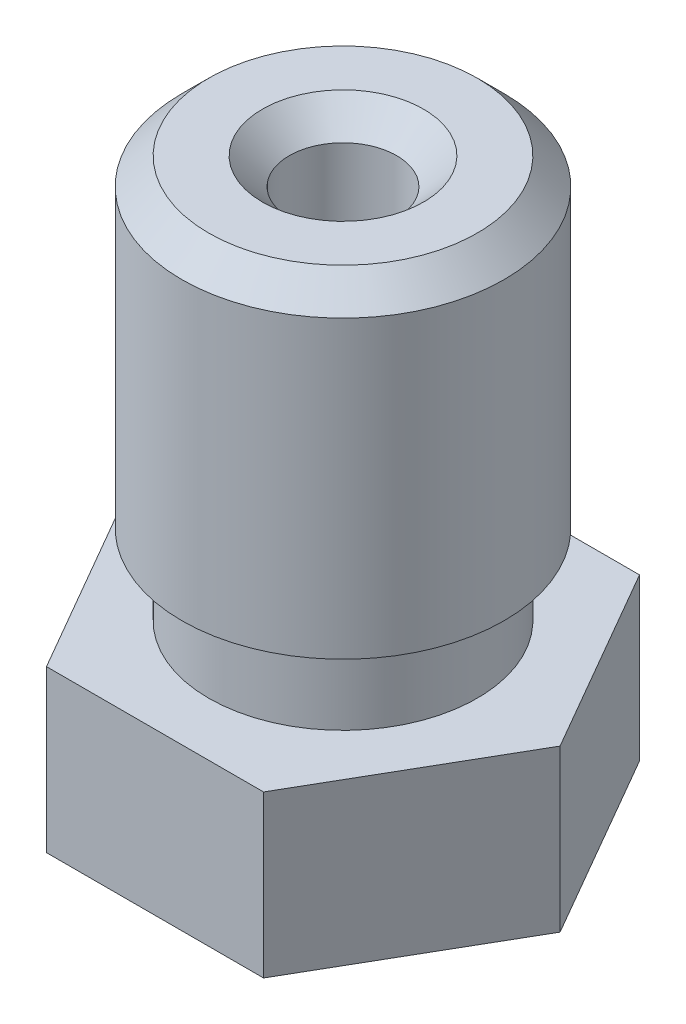
SolidWorks part; units mm, degrees
material "Brass"
ref_plane "Front Plane" through (0, 0, 0) normal (0, 0, 1) x (1, 0, 0)
ref_plane "Top Plane" through (0, 0, 0) normal (0, 1, 0) x (1, 0, 0)
ref_plane "Right Plane" through (0, 0, 0) normal (1, 0, 0) x (0, 0, -1)
ref_plane "Plane1" through (0, 0, 0) normal (0, -1, 0) x (1, 0, 0)
sketch "Sketch1" plane through (0, 0, 0) normal (0, -1, 0) x (1, 0, 0)
  line L0 (-2.0207, 3.5) -> (-4.0415, 0)
  line L1 (-4.0415, 0) -> (-2.0207, -3.5)
  line L2 (-2.0207, -3.5) -> (2.0207, -3.5)
  line L3 (2.0207, -3.5) -> (4.0415, 0)
  line L4 (4.0415, 0) -> (2.0207, 3.5)
  line L5 (2.0207, 3.5) -> (-2.0207, 3.5)
extrude "Boss-Extrude1" add sketch "Sketch1" against normal blind 3
ref_plane "Plane2" through (0, 0, 0) normal (0, 0, -1) x (-1, 0, 0)
sketch "Sketch2" plane through (0, 0, 0) normal (0, 0, -1) x (-1, 0, 0)
  line L0 (-2.5, 3) -> (0, 3)
  line L1 (0, 3) -> (0, 10.5)
  line L2 (0, 10.5) -> (-3, 10.5)
  line L3 (-3, 10.5) -> (-3, 4.5)
  line L4 (-3, 4.5) -> (-2.5, 4.5)
  line L5 (-2.5, 4.5) -> (-2.5, 3)
  line L6 (0, 3) -> (0, 10.5) construction
revolve "Revolve1" add sketch "Sketch2" angle 360 about L6
sketch "Sketch3" plane through (0, 0, 0) normal (0, 0, 1) x (1, 0, 0)
  line L0 (2.5, 0) -> (0, 0)
  line L1 (0, 0) -> (0, -2)
  line L2 (0, -2) -> (0.5, -2)
  line L3 (0.5, -2) -> (2.5, 0)
  line L4 (0, 0) -> (0, -2) construction
revolve "Revolve2" add sketch "Sketch3" angle 360 about L4
sketch "Sketch4" plane through (0, 0, 0) normal (0, 0, -1) x (-1, 0, 0)
  line L0 (-0.2, -2) -> (0, -2)
  line L1 (0, -2) -> (0, 10.5)
  line L2 (0, 10.5) -> (-1, 10.5)
  line L3 (-1, 10.5) -> (-1, 0)
  line L4 (-1, 0) -> (-0.75, -0.2273)
  line L5 (-0.75, -0.2273) -> (-0.75, -0.7)
  line L6 (-0.75, -0.7) -> (-0.2, -1.2)
  line L7 (-0.2, -1.2) -> (-0.2, -2)
  line L8 (0, -2) -> (0, 10.5) construction
revolve "Cut-Revolve1" cut sketch "Sketch4" angle 360 about L8
chamfer "Chamfer1" distance 0.5 angle 45 2 edges at (0, 10.5, 3) (0, 10.5, 1)
